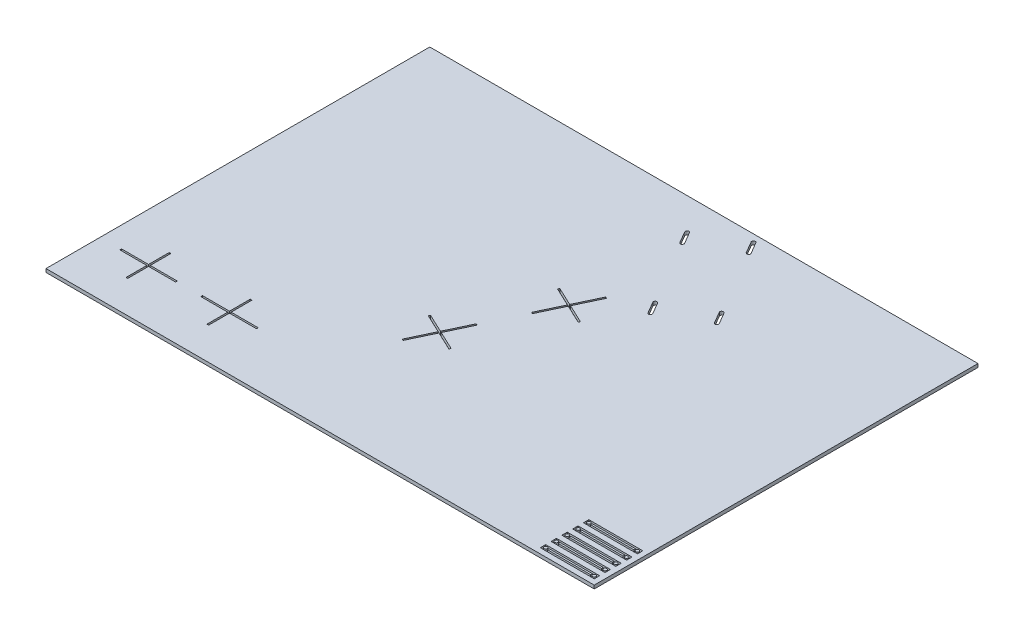
SolidWorks part; units mm, degrees
material "FiberBoard"
ref_plane "Front Plane" through (0, 0, 0) normal (0, 0, 1) x (1, 0, 0)
ref_plane "Top Plane" through (0, 0, 0) normal (0, 1, 0) x (1, 0, 0)
ref_plane "Right Plane" through (0, 0, 0) normal (1, 0, 0) x (0, 0, -1)
sketch "Sketch1" plane through (0, 0, 0) normal (0, 1, 0) x (1, 0, 0)
  line L1 (0, 0) -> (1016, 0)
  line L2 (0, 0) -> (0, -711.2)
  line L3 (0, -711.2) -> (1016, -711.2)
  line L4 (1016, 0) -> (1016, -711.2)
  dimension "D1" = 1016
  dimension "D2" = 711.2
extrude "Boss-Extrude1" add sketch "Sketch1" along normal blind 6.35
sketch "Sketch2" plane through (0, 6.35, 0) normal (0, 1, 0) x (1, 0, 0)
  line L0 (0, -611.2) -> (390, -611.2) construction
  line L1 (0, 0) -> (0, -711.2) construction
  line L2 (390, -611.2) -> (622.6561, -118.2378) construction
  line L3 (0, -711.2) -> (1016, -711.2) construction
  line L4 (593.6049, -68.6165) -> (651.7073, -167.8591) construction
  line L5 (431.3295, -429.9105) -> (503.6768, -464.0552)
  line L6 (88.4125, -571.2) -> (91.5875, -571.2)
  line L7 (88.4125, -571.2) -> (88.4125, -651.2)
  line L8 (88.4125, -651.2) -> (91.5875, -651.2)
  line L9 (91.5875, -571.2) -> (91.5875, -651.2)
  line L10 (88.4125, -571.2) -> (91.5875, -651.2) construction
  line L11 (88.4125, -651.2) -> (91.5875, -571.2) construction
  line L12 (238.4125, -571.2) -> (241.5875, -571.2)
  line L13 (238.4125, -571.2) -> (238.4125, -651.2)
  line L14 (238.4125, -651.2) -> (241.5875, -651.2)
  line L15 (241.5875, -571.2) -> (241.5875, -651.2)
  line L16 (238.4125, -571.2) -> (241.5875, -651.2) construction
  line L17 (238.4125, -651.2) -> (241.5875, -571.2) construction
  line L18 (431.3295, -429.9105) -> (429.9744, -432.7818)
  line L19 (503.6768, -464.0552) -> (502.3217, -466.9265)
  line L20 (429.9744, -432.7818) -> (502.3217, -466.9265)
  line L21 (431.3295, -429.9105) -> (502.3217, -466.9265) construction
  line L22 (503.6768, -464.0552) -> (429.9744, -432.7818) construction
  line L23 (508.1551, -267.1289) -> (580.5024, -301.2737)
  line L24 (508.1551, -267.1289) -> (506.8, -270.0002)
  line L25 (580.5024, -301.2737) -> (579.1473, -304.1449)
  line L26 (506.8, -270.0002) -> (579.1473, -304.1449)
  line L27 (508.1551, -267.1289) -> (579.1473, -304.1449) construction
  line L28 (580.5024, -301.2737) -> (506.8, -270.0002) construction
  line L29 (545.6527, -65.8815) -> (614.6911, -25.4624) construction
  line L30 (545.6527, -65.8815) -> (547.2568, -68.6215) construction
  line L31 (614.6911, -25.4624) -> (616.2952, -28.2024) construction
  line L32 (547.2568, -68.6215) -> (616.2952, -28.2024) construction
  line L33 (545.6527, -65.8815) -> (616.2952, -28.2024) construction
  line L34 (614.6911, -25.4624) -> (547.2568, -68.6215) construction
  line L35 (698.0554, -167.8541) -> (629.0171, -208.2732) construction
  line L36 (698.0554, -167.8541) -> (699.6596, -170.5941) construction
  line L37 (629.0171, -208.2732) -> (630.6212, -211.0131) construction
  line L38 (699.6596, -170.5941) -> (630.6212, -211.0131) construction
  line L39 (698.0554, -167.8541) -> (630.6212, -211.0131) construction
  line L40 (629.0171, -208.2732) -> (699.6596, -170.5941) construction
  line L41 (651.7073, -167.8591) -> (664.3383, -189.4336) construction
  line L42 (593.6049, -68.6165) -> (580.974, -47.042) construction
  line L43 (535.8244, -58.9904) -> (548.4553, -80.5649) construction
  line L44 (538.6291, -57.3484) -> (551.26, -78.9229)
  line L45 (533.0197, -60.6325) -> (545.6507, -82.207)
  line L46 (546.4548, -67.2515) -> (542.1399, -69.7777) construction
  line L47 (589.2311, -137.8067) -> (656.0811, -98.6689) construction
  line L48 (613.4926, -13.519) -> (626.1235, -35.0935) construction
  line L51 (616.2972, -11.877) -> (628.9282, -33.4514)
  line L52 (610.6879, -15.161) -> (623.3188, -36.7355)
  line L53 (538.6291, -57.3484) -> (610.6879, -15.161) construction
  line L54 (709.4879, -177.4851) -> (696.8569, -155.9106) construction
  line L55 (712.2926, -175.8431) -> (699.6616, -154.2686)
  line L56 (706.6832, -179.1272) -> (694.0522, -157.5527)
  line L57 (631.8197, -222.9566) -> (619.1887, -201.3821) construction
  line L58 (634.6244, -221.3146) -> (621.9934, -199.7401)
  line L59 (629.015, -224.5986) -> (616.3841, -203.0241)
  arc A0 (538.6291, -57.3484) -> (533.0197, -60.6325) centre (535.8244, -58.9904) ccw
  arc A1 (545.6507, -82.207) -> (551.26, -78.9229) centre (548.4553, -80.5649) ccw
  arc A4 (616.2972, -11.877) -> (610.6879, -15.161) centre (613.4926, -13.519) ccw
  arc A5 (623.3188, -36.7355) -> (628.9282, -33.4514) centre (626.1235, -35.0935) ccw
  arc A6 (712.2926, -175.8431) -> (706.6832, -179.1272) centre (709.4879, -177.4851) cw
  arc A7 (694.0522, -157.5527) -> (699.6616, -154.2686) centre (696.8569, -155.9106) cw
  arc A8 (634.6244, -221.3146) -> (629.015, -224.5986) centre (631.8197, -222.9566) cw
  arc A9 (616.3841, -203.0241) -> (621.9934, -199.7401) centre (619.1887, -201.3821) cw
  point P9 (622.6561, -118.2378)
  point P10 (90, -611.2)
  point P15 (240, -611.2)
  point P21 (466.8256, -448.4185)
  point P22 (543.6512, -285.6369)
  point P23 (580.974, -47.042)
  point P28 (664.3383, -189.4336)
  point P44 (542.1399, -69.7777)
  point P55 (619.808, -24.3062)
  point P61 (622.6561, -118.2378)
  point P65 (703.1724, -166.6979)
  point P72 (625.5042, -212.1693)
  dimension "D15" = 3.25
  dimension "D19" = 3.25
  dimension "D1" = 390
  dimension "D2" = 100
  dimension "D3" = 545.1061
  dimension "D4" = 64.735
  dimension "D5" = 115
  dimension "D6" = 124.388
  dimension "D7" = 80
  dimension "D8" = 3.175
  dimension "D9" = 90
  dimension "D10" = 240
  dimension "D11" = 180
  dimension "D12" = 360
  dimension "D13" = 25
  dimension "D14" = 25
  dimension "D16" = 5
  dimension "D17" = 83.5
  dimension "D18" = 25
extrude "Cut-Extrude1" cut sketch "Sketch2" against normal blind 6.35
sketch "Sketch4" plane through (0, 6.35, 0) normal (0, 1, 0) x (1, 0, 0)
  line L0 (506.8, -270.0002) -> (579.1473, -304.1449) construction
  line L1 (580.5024, -301.2737) -> (508.1551, -267.1289) construction
  line L2 (503.6768, -464.0552) -> (431.3295, -429.9105) construction
  line L3 (429.9744, -432.7818) -> (502.3217, -466.9265) construction
  line L4 (241.5875, -651.2) -> (241.5875, -571.2) construction
  line L5 (238.4125, -571.2) -> (238.4125, -651.2) construction
  line L6 (88.4125, -571.2) -> (88.4125, -651.2) construction
  line L7 (91.5875, -651.2) -> (91.5875, -571.2) construction
  line L8 (506.8, -270.0002) -> (579.1473, -304.1449) construction
  line L9 (580.5024, -301.2737) -> (508.1551, -267.1289) construction
  line L10 (503.6768, -464.0552) -> (431.3295, -429.9105) construction
  line L11 (429.9744, -432.7818) -> (502.3217, -466.9265) construction
  line L12 (241.5875, -651.2) -> (241.5875, -571.2) construction
  line L13 (238.4125, -571.2) -> (238.4125, -651.2) construction
  line L14 (88.4125, -571.2) -> (88.4125, -651.2) construction
  line L15 (91.5875, -651.2) -> (91.5875, -571.2) construction
  line L16 (467.5837, -450.5317) -> (446.2432, -495.7488)
  line L17 (38.4125, -609.6125) -> (88.4125, -609.6125)
  line L18 (38.4125, -609.6125) -> (38.4125, -612.7875)
  line L19 (38.4125, -612.7875) -> (88.4125, -612.7875)
  line L20 (88.4125, -609.6125) -> (88.4125, -612.7875)
  line L21 (38.4125, -609.6125) -> (88.4125, -612.7875) construction
  line L22 (38.4125, -612.7875) -> (88.4125, -609.6125) construction
  line L23 (91.5875, -609.6125) -> (141.5875, -609.6125)
  line L24 (91.5875, -609.6125) -> (91.5875, -612.7875)
  line L25 (91.5875, -612.7875) -> (141.5875, -612.7875)
  line L26 (141.5875, -609.6125) -> (141.5875, -612.7875)
  line L27 (91.5875, -609.6125) -> (141.5875, -612.7875) construction
  line L28 (91.5875, -612.7875) -> (141.5875, -609.6125) construction
  line L29 (188.4125, -612.7875) -> (238.4125, -612.7875)
  line L30 (188.4125, -612.7875) -> (188.4125, -609.6125)
  line L31 (188.4125, -609.6125) -> (238.4125, -609.6125)
  line L32 (238.4125, -612.7875) -> (238.4125, -609.6125)
  line L33 (188.4125, -612.7875) -> (238.4125, -609.6125) construction
  line L34 (188.4125, -609.6125) -> (238.4125, -612.7875) construction
  line L35 (241.5875, -609.6125) -> (291.5875, -609.6125)
  line L36 (241.5875, -609.6125) -> (241.5875, -612.7875)
  line L37 (241.5875, -612.7875) -> (291.5875, -612.7875)
  line L38 (291.5875, -609.6125) -> (291.5875, -612.7875)
  line L39 (241.5875, -609.6125) -> (291.5875, -612.7875) construction
  line L40 (241.5875, -612.7875) -> (291.5875, -609.6125) construction
  line L41 (467.5837, -450.5317) -> (464.7124, -449.1766)
  line L42 (446.2432, -495.7488) -> (443.372, -494.3936)
  line L43 (464.7124, -449.1766) -> (443.372, -494.3936)
  line L44 (467.5837, -450.5317) -> (443.372, -494.3936) construction
  line L45 (446.2432, -495.7488) -> (464.7124, -449.1766) construction
  line L46 (431.3295, -429.9105) -> (429.9744, -432.7818) construction
  line L47 (487.408, -401.0882) -> (466.0675, -446.3053)
  line L48 (487.408, -401.0882) -> (490.2793, -402.4433)
  line L49 (466.0675, -446.3053) -> (468.9388, -447.6604)
  line L50 (490.2793, -402.4433) -> (468.9388, -447.6604)
  line L51 (487.408, -401.0882) -> (468.9388, -447.6604) construction
  line L52 (466.0675, -446.3053) -> (490.2793, -402.4433) construction
  line L53 (541.538, -286.395) -> (520.1976, -331.6121)
  line L54 (541.538, -286.395) -> (544.4093, -287.7501)
  line L55 (520.1976, -331.6121) -> (523.0688, -332.9672)
  line L56 (544.4093, -287.7501) -> (523.0688, -332.9672)
  line L57 (541.538, -286.395) -> (523.0688, -332.9672) construction
  line L58 (520.1976, -331.6121) -> (544.4093, -287.7501) construction
  line L59 (564.2336, -238.3066) -> (542.8931, -283.5237)
  line L60 (564.2336, -238.3066) -> (567.1049, -239.6618)
  line L61 (542.8931, -283.5237) -> (545.7644, -284.8789)
  line L62 (567.1049, -239.6618) -> (545.7644, -284.8789)
  line L63 (564.2336, -238.3066) -> (545.7644, -284.8789) construction
  line L64 (542.8931, -283.5237) -> (567.1049, -239.6618) construction
  point P16 (63.4125, -611.2)
  point P21 (88.4125, -611.2)
  point P22 (88.4125, -611.2)
  point P23 (116.5875, -611.2)
  point P28 (91.5875, -611.2)
  point P29 (91.5875, -611.2)
  point P30 (213.4125, -611.2)
  point P35 (266.5875, -611.2)
  point P40 (238.4125, -611.2)
  point P41 (238.4125, -611.2)
  point P42 (241.5875, -611.2)
  point P43 (241.5875, -611.2)
  point P45 (455.4778, -472.4627)
  point P47 (466.148, -449.8541)
  point P52 (466.148, -449.8541)
  point P53 (467.5032, -446.9828)
  point P54 (478.1734, -424.3743)
  point P55 (467.5032, -446.9828)
  point P56 (544.3288, -284.2013)
  point P61 (532.3034, -309.6811)
  point P62 (554.999, -261.5928)
  point P63 (544.3288, -284.2013)
  point P68 (542.9737, -287.0726)
  point P73 (542.9737, -287.0726)
  dimension "D1" = 50
  dimension "D2" = 3.175
extrude "Cut-Extrude2" cut sketch "Sketch4" against normal blind 10
sketch "Sketch5" plane through (0, 6.35, 0) normal (0, 1, 0) x (1, 0, 0)
  line L0 (0, -711.2) -> (1016, -711.2) construction
  line L1 (906, -691.2) -> (1006, -691.2)
  line L2 (906, -691.2) -> (906, -701.2)
  line L3 (906, -701.2) -> (1006, -701.2)
  line L4 (1006, -691.2) -> (1006, -701.2)
  line L5 (906, -691.2) -> (1006, -701.2) construction
  line L6 (906, -701.2) -> (1006, -691.2) construction
  line L7 (916, -694.6125) -> (996, -694.6125)
  line L8 (916, -694.6125) -> (916, -697.7875)
  line L9 (916, -697.7875) -> (996, -697.7875)
  line L10 (996, -694.6125) -> (996, -697.7875)
  line L11 (916, -694.6125) -> (996, -697.7875) construction
  line L12 (916, -697.7875) -> (996, -694.6125) construction
  line L13 (1016, -711.2) -> (1016, 0) construction
  line L14 (911, -696.2) -> (906, -696.2) construction
  line L15 (906, -671.2) -> (1006, -671.2)
  line L16 (906, -671.2) -> (906, -681.2)
  line L17 (906, -681.2) -> (1006, -681.2)
  line L18 (1006, -671.2) -> (1006, -681.2)
  line L19 (906, -671.2) -> (1006, -681.2) construction
  line L20 (906, -681.2) -> (1006, -671.2) construction
  line L21 (916, -674.6125) -> (996, -674.6125)
  line L22 (916, -674.6125) -> (916, -677.7875)
  line L23 (916, -677.7875) -> (996, -677.7875)
  line L24 (996, -674.6125) -> (996, -677.7875)
  line L25 (916, -674.6125) -> (996, -677.7875) construction
  line L26 (916, -677.7875) -> (996, -674.6125) construction
  line L27 (911, -676.2) -> (906, -676.2) construction
  line L28 (1006, -676.2) -> (1001, -676.2) construction
  line L29 (906, -651.2) -> (1006, -651.2)
  line L30 (906, -651.2) -> (906, -661.2)
  line L31 (906, -661.2) -> (1006, -661.2)
  line L32 (1006, -651.2) -> (1006, -661.2)
  line L33 (906, -651.2) -> (1006, -661.2) construction
  line L34 (906, -661.2) -> (1006, -651.2) construction
  line L35 (916, -654.6125) -> (996, -654.6125)
  line L36 (916, -654.6125) -> (916, -657.7875)
  line L37 (916, -657.7875) -> (996, -657.7875)
  line L38 (996, -654.6125) -> (996, -657.7875)
  line L39 (916, -654.6125) -> (996, -657.7875) construction
  line L40 (916, -657.7875) -> (996, -654.6125) construction
  line L41 (911, -656.2) -> (906, -656.2) construction
  line L42 (1006, -656.2) -> (1001, -656.2) construction
  line L43 (906, -611.2) -> (1006, -611.2)
  line L44 (906, -611.2) -> (906, -621.2)
  line L45 (906, -621.2) -> (1006, -621.2)
  line L46 (1006, -611.2) -> (1006, -621.2)
  line L47 (906, -611.2) -> (1006, -621.2) construction
  line L48 (906, -621.2) -> (1006, -611.2) construction
  line L49 (916, -614.6125) -> (996, -614.6125)
  line L50 (916, -614.6125) -> (916, -617.7875)
  line L51 (916, -617.7875) -> (996, -617.7875)
  line L52 (996, -614.6125) -> (996, -617.7875)
  line L53 (916, -614.6125) -> (996, -617.7875) construction
  line L54 (916, -617.7875) -> (996, -614.6125) construction
  line L55 (911, -616.2) -> (906, -616.2) construction
  line L56 (1006, -616.2) -> (1001, -616.2) construction
  line L57 (906, -631.2) -> (1006, -631.2)
  line L58 (906, -631.2) -> (906, -641.2)
  line L59 (906, -641.2) -> (1006, -641.2)
  line L60 (1006, -631.2) -> (1006, -641.2)
  line L61 (906, -631.2) -> (1006, -641.2) construction
  line L62 (906, -641.2) -> (1006, -631.2) construction
  line L63 (916, -634.6125) -> (996, -634.6125)
  line L64 (916, -634.6125) -> (916, -637.7875)
  line L65 (916, -637.7875) -> (996, -637.7875)
  line L66 (996, -634.6125) -> (996, -637.7875)
  line L67 (916, -634.6125) -> (996, -637.7875) construction
  line L68 (916, -637.7875) -> (996, -634.6125) construction
  line L69 (911, -636.2) -> (906, -636.2) construction
  line L70 (1006, -636.2) -> (1001, -636.2) construction
  line L71 (1006, -701.2) -> (1006, -711.2) construction
  line L72 (1006, -681.2) -> (1006, -691.2) construction
  line L73 (1006, -671.2) -> (1006, -661.2) construction
  line L74 (1006, -651.2) -> (1006, -641.2) construction
  line L75 (1006, -631.2) -> (1006, -621.2) construction
  circle A0 centre (911, -696.2) radius 3
  circle A1 centre (1001, -696.2) radius 3
  circle A2 centre (911, -676.2) radius 3
  circle A3 centre (1001, -676.2) radius 3
  circle A4 centre (911, -656.2) radius 3
  circle A5 centre (1001, -656.2) radius 3
  circle A6 centre (911, -616.2) radius 3
  circle A7 centre (1001, -616.2) radius 3
  circle A8 centre (911, -636.2) radius 3
  circle A9 centre (1001, -636.2) radius 3
  point P0 (956, -696.2)
  point P9 (956, -696.2)
  point P18 (916, -696.2)
  point P19 (996, -696.2)
  point P20 (956, -676.2)
  point P25 (956, -676.2)
  point P37 (956, -656.2)
  point P42 (956, -656.2)
  point P53 (956, -616.2)
  point P58 (956, -616.2)
  point P69 (956, -636.2)
  point P74 (956, -636.2)
  dimension "D7" = 6
  dimension "D1" = 100
  dimension "D2" = 10
  dimension "D3" = 80
  dimension "D4" = 3.175
  dimension "D5" = 5
  dimension "D6" = 5
  dimension "D8" = 10
  dimension "D9" = 10
extrude "Cut-Extrude3" cut sketch "Sketch5" against normal blind 10 contours A4 | L29 L32 L31 L30 | L57 L60 L59 L58 | A8 | A9 | A7 | A6 | L49 L52 L51 L50 | L43 L46 L45 L44 | L63 L66 L65 L64 | L16 L15 L18 L17 | A2 | L22 L21 L24 L23 | A3 | L2 L1 L4 L3 | A1 | L8 L7 L10 L9 | A0 | L35 L38 L37 L36 | A5
